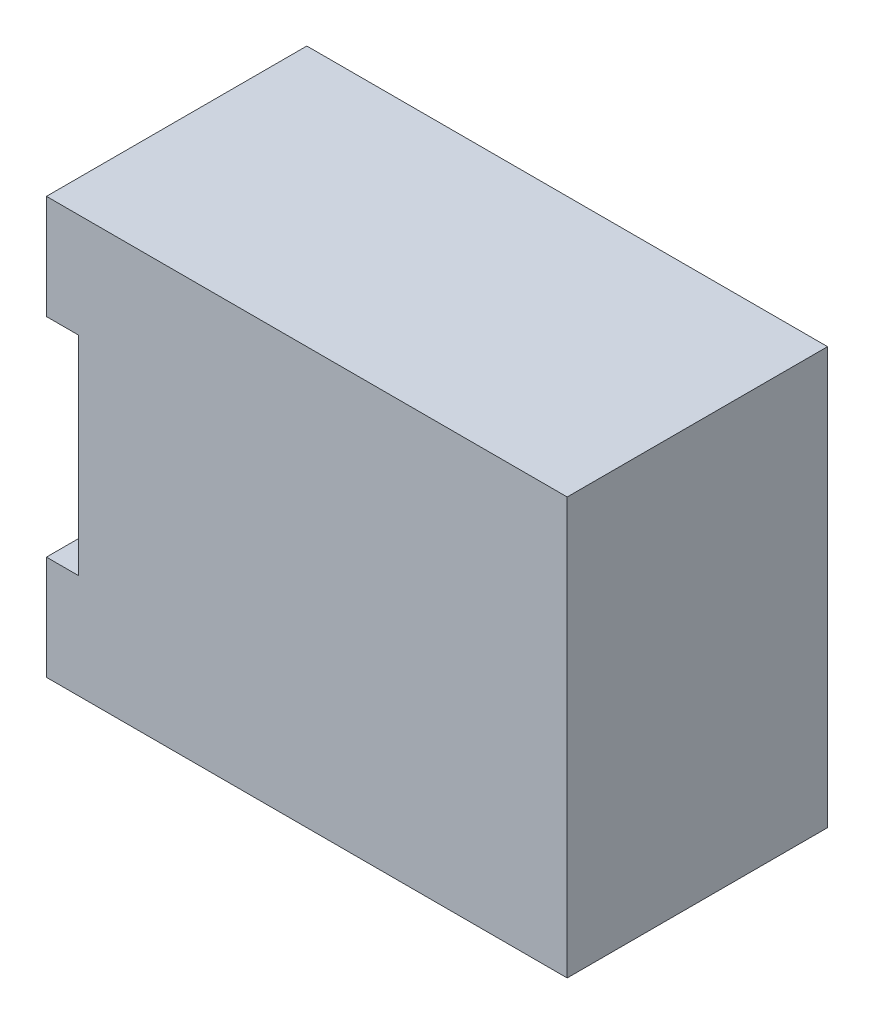
SolidWorks part; units mm, degrees
ref_plane "Plano frontal" through (0, 0, 0) normal (0, 0, 1) x (1, 0, 0)
ref_plane "Plano superior" through (0, 0, 0) normal (0, 1, 0) x (1, 0, 0)
ref_plane "Plano direito" through (0, 0, 0) normal (1, 0, 0) x (0, 0, -1)
sketch "Esboço1" plane through (0, 0, 0) normal (0, 0, 1) x (1, 0, 0)
  line L0 (-40.9758, 17.3333) -> (-36.9758, 17.3333)
  line L1 (-40.9758, 30.3333) -> (24.0242, 30.3333)
  line L2 (-40.9758, 30.3333) -> (-40.9758, 17.3333)
  line L3 (-40.9758, -21.6667) -> (24.0242, -21.6667)
  line L4 (24.0242, 30.3333) -> (24.0242, -21.6667)
  line L5 (-36.9758, 17.3333) -> (-36.9758, -8.6667)
  line L6 (-36.9758, -8.6667) -> (-40.9758, -8.6667)
  line L7 (-40.9758, -8.6667) -> (-40.9758, -21.6667)
  dimension "D1" = 52
  dimension "D2" = 65
  dimension "D3" = 61
  dimension "D4" = 13
  dimension "D5" = 13
extrude "Ressalto-extrusão1" add sketch "Esboço1" along normal blind 32.5
